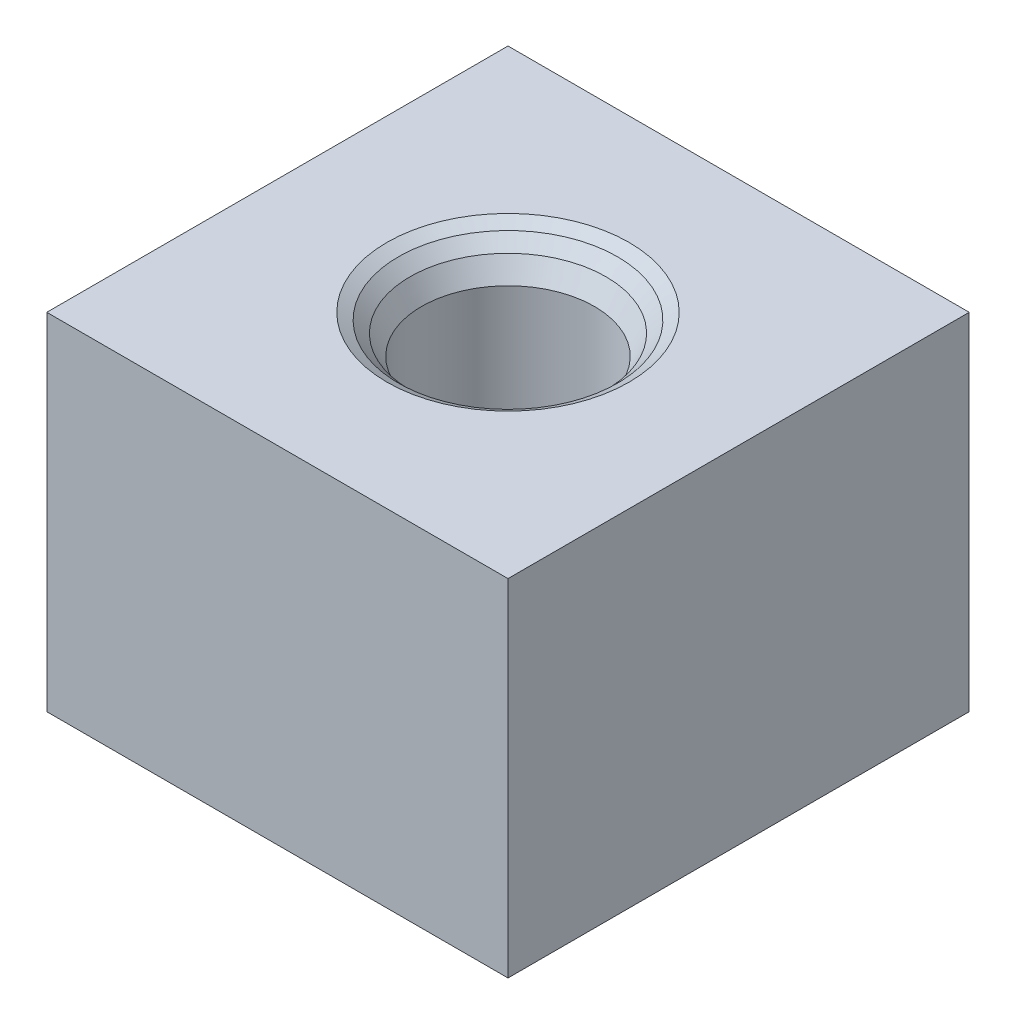
SolidWorks part; units mm, degrees
ref_plane "Front Plane" through (0, 0, 0) normal (0, 0, 1) x (1, 0, 0)
ref_plane "Top Plane" through (0, 0, 0) normal (0, 1, 0) x (1, 0, 0)
ref_plane "Right Plane" through (0, 0, 0) normal (1, 0, 0) x (0, 0, -1)
sketch "Sketch1" plane through (0, 0, 0) normal (0, 1, 0) x (1, 0, 0)
  line L1 (-40, -40) -> (40, -40)
  line L2 (-40, -40) -> (-40, 40)
  line L3 (-40, 40) -> (40, 40)
  line L4 (40, -40) -> (40, 40)
  line L5 (-40, -40) -> (40, 40) construction
  line L6 (-40, 40) -> (40, -40) construction
  point P0 (0, 0)
  dimension "D1" = 80
  dimension "D2" = 80
extrude "Boss-Extrude1" add sketch "Sketch1" along normal blind 60
sketch "Sketch2" plane through (0, 0, 0) normal (0, 0, 1) x (1, 0, 0)
  line L0 (40, 60) -> (0, 60) construction
  line L1 (-40, 60) -> (40, 60) construction
  line L2 (0, 60) -> (-21, 60)
  line L3 (-21, 60) -> (-19, 58.8453)
  line L4 (-19, 58.8453) -> (-17, 56.8453)
  line L5 (-15, 10) -> (0, 10)
  line L6 (0, 10) -> (0, 60)
  line L7 (-17, 56.8453) -> (-15, 53.3812)
  line L8 (-19, 58.8453) -> (-19, 60) construction
  line L9 (-17, 56.8453) -> (-17, 60) construction
  line L10 (-15, 53.3812) -> (-15, 60) construction
  line L11 (-15, 53.3812) -> (-15, 10)
  dimension "D1" = 50
  dimension "D2" = 60
  dimension "D4" = 40
  dimension "D5" = 21
  dimension "D6" = 45
  dimension "D7" = 30
  dimension "D8" = 19
  dimension "D9" = 17
  dimension "D10" = 15
revolve "Cut-Revolve1" cut sketch "Sketch2" angle 360 about L6
